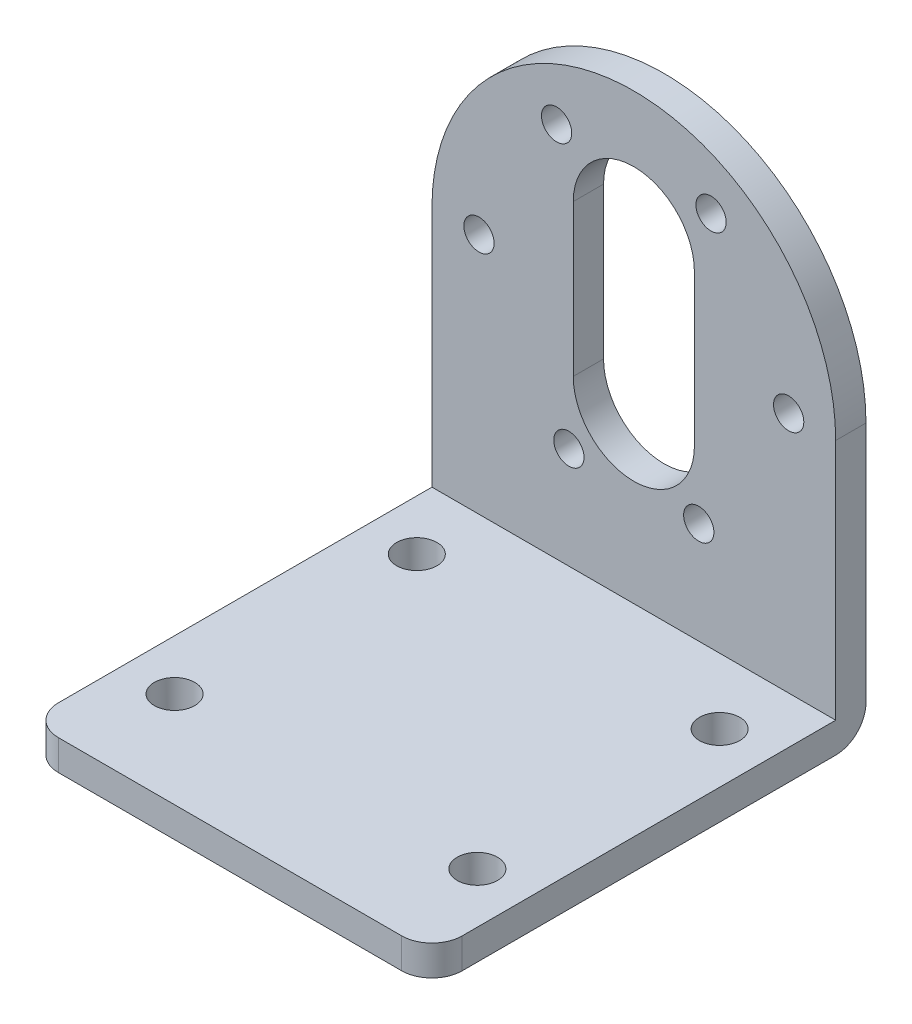
SolidWorks part; units mm, degrees
ref_plane "Front Plane" through (0, 0, 0) normal (0, 0, 1) x (1, 0, 0)
ref_plane "Top Plane" through (0, 0, 0) normal (0, 1, 0) x (1, 0, 0)
ref_plane "Right Plane" through (0, 0, 0) normal (1, 0, 0) x (0, 0, -1)
sketch "Sketch3" plane through (0, 0, 0) normal (0, 1, 0) x (1, 0, 0)
  line L1 (20, -21.5) -> (-20, -21.5)
  line L2 (20, -21.5) -> (20, 21.5)
  line L3 (20, 21.5) -> (-20, 21.5)
  line L4 (-20, -21.5) -> (-20, 21.5)
  line L5 (20, -21.5) -> (-20, 21.5) construction
  line L6 (20, 21.5) -> (-20, -21.5) construction
  point P0 (0, 0)
extrude "Boss-Extrude1" add sketch "Sketch3" along normal blind 3
sketch "Sketch4" plane through (0, 3, 0) normal (0, 1, 0) x (1, 0, 0)
  line L0 (20, -21.5) -> (20, 21.5) construction
  line L1 (-20, 21.5) -> (20, 21.5)
  line L2 (-20, 21.5) -> (-20, 18.5)
  line L3 (-20, 18.5) -> (20, 18.5)
  line L4 (20, 21.5) -> (20, 18.5)
extrude "Boss-Extrude2" add sketch "Sketch4" along normal blind 24
sketch "Sketch6" plane through (0, 0, -18.5) normal (0, 0, 1) x (1, 0, 0)
  line L0 (-20, 27) -> (20, 27) construction
  circle A0 centre (0, 27) radius 20
extrude "Boss-Extrude3" add sketch "Sketch6" against normal blind 3
sketch "Sketch7" plane through (0, 0, -18.5) normal (0, 0, 1) x (1, 0, 0)
  circle A0 centre (0, 27) radius 15.34
  circle A1 centre (7.65, 40.2964) radius 1.5
  circle A2 centre (15.34, 27) radius 1.5
  circle A4 centre (6.4329, 13.074) radius 1.5
  dimension "D1" = 7.65
extrude "Cut-Extrude1" cut sketch "Sketch7" against normal blind 8 contours A0 A1 | A0 A1 | A0 A2 | A0 A4 | A0 A4 | A0 A2
mirror "Mirror1" about plane through (0, 0, 0) normal (1, 0, 0) of "Cut-Extrude1"
fillet "Fillet1" radius 3 1 edges at (0, 0, -21.5)
sketch "Sketch8" plane through (0, 3, 0) normal (0, 1, 0) x (1, 0, 0)
  circle A0 centre (-15, 12) radius 2
  dimension "D1" = 15
  dimension "D2" = 12
extrude "Cut-Extrude2" cut sketch "Sketch8" against normal blind 8
mirror "Mirror2" about plane through (0, 0, 0) normal (1, 0, 0) of "Cut-Extrude2"
mirror "Mirror3" about plane through (0, 0, 0) normal (0, 0, 1) of "Mirror2", "Cut-Extrude2"
fillet "Fillet2" radius 3 2 edges at (20, 1.5, 21.5) (-20, 1.5, 21.5)
sketch "Sketch9" plane through (0, 0, -18.5) normal (0, 0, 1) x (1, 0, 0)
  line L0 (0, 34.5) -> (0, 19.5) construction
  line L1 (6, 34.5) -> (6, 19.5)
  line L2 (-6, 34.5) -> (-6, 19.5)
  arc A0 (6, 34.5) -> (-6, 34.5) centre (0, 34.5) ccw
  arc A1 (-6, 19.5) -> (6, 19.5) centre (0, 19.5) ccw
  arc A2 (20, 27) -> (-20, 27) centre (0, 27) ccw construction
  point P3 (0, 27)
  dimension "D1" = 0
extrude "Cut-Extrude3" cut sketch "Sketch9" against normal blind 8
